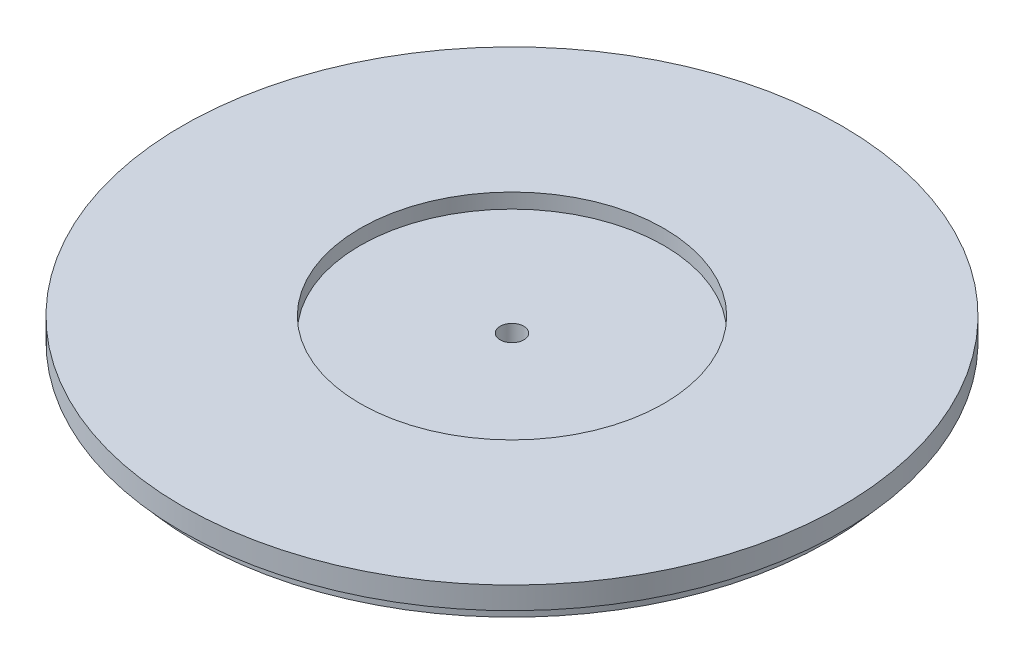
SolidWorks part; units mm, degrees
material "A-Glasfaser"
ref_plane "Ebene vorne" through (0, 0, 0) normal (0, 0, 1) x (1, 0, 0)
ref_plane "Ebene oben" through (0, 0, 0) normal (0, 1, 0) x (1, 0, 0)
ref_plane "Ebene rechts" through (0, 0, 0) normal (1, 0, 0) x (0, 0, -1)
sketch "Skizze2" plane through (0, 0, 0) normal (0, 0, 1) x (1, 0, 0)
  line L0 (-1.6, 0) -> (-1.6, 3)
  line L1 (-1.6, 3) -> (-20.5, 3)
  line L2 (-20.5, 3) -> (-20.5, 5)
  line L3 (-20.5, 5) -> (-44.5, 5)
  line L4 (-44.5, 5) -> (-44.5, 2)
  line L5 (-44.5, 2) -> (-42.75, 2)
  line L6 (-42.75, 2) -> (-42.75, 0)
  line L7 (-42.75, 0) -> (-1.6, 0)
  line L8 (0, -1.7415) -> (0, 1.4865) construction
  dimension "D1" = 1.6
  dimension "D2" = 2
  dimension "D3" = 5
  dimension "D4" = 44.5
  dimension "D5" = 42.75
  dimension "D6" = 20.5
revolve "Rotation1" add sketch "Skizze2" angle 360 about L8
